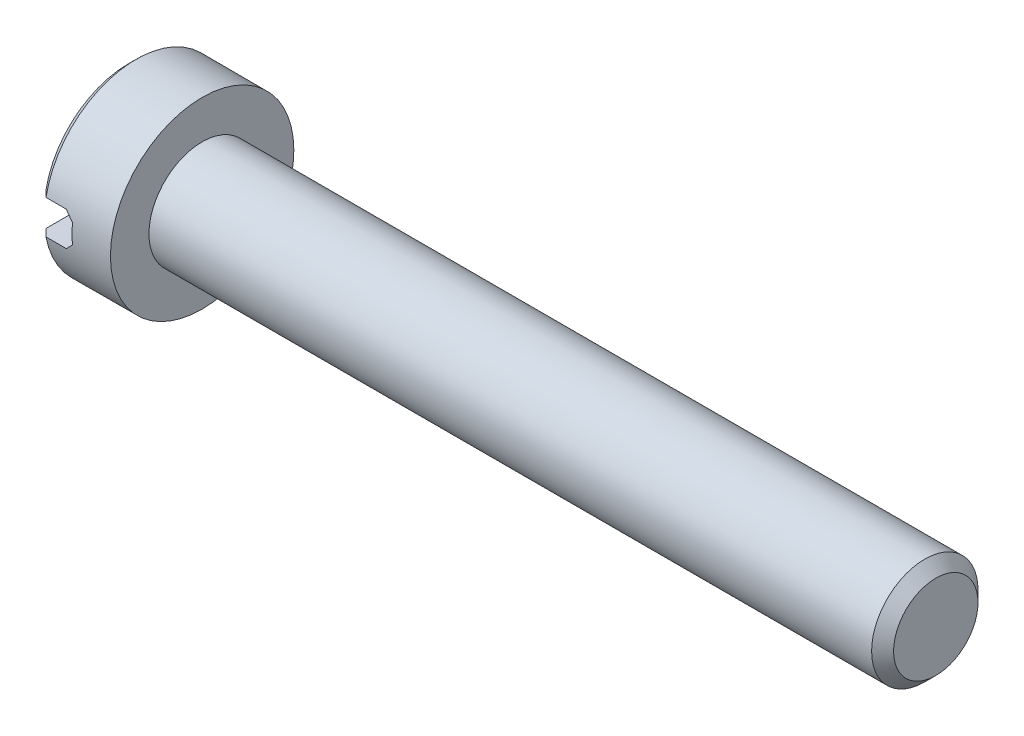
SolidWorks part; units mm, degrees
ref_plane "Face" through (0, 0, 0) normal (0, 0, 1) x (1, 0, 0)
ref_plane "Dessus" through (0, 0, 0) normal (0, 1, 0) x (1, 0, 0)
ref_plane "Droite" through (0, 0, 0) normal (1, 0, 0) x (0, 0, -1)
sketch "Esquisse1" plane through (0, 0, 0) normal (0, 0, 1) x (1, 0, 0)
  line L0 (0, 0) -> (0, 2.3)
  line L1 (0.2, 2.5) -> (2, 2.5)
  line L2 (2, 2.5) -> (2, 0)
  line L5 (0, 0) -> (7.6423, 0) construction
  line L7 (0, 2.3) -> (0.2, 2.5)
  line L8 (0, 0) -> (2, 0)
  point P1 (0, 2.5)
  dimension "D1" = 2.5
  dimension "D3" = 2
  dimension "D9" = 0.2
revolve "Révolution1" add sketch "Esquisse1" angle 360 about L5
sketch "Esquisse2" plane through (0, 0, 0) normal (0, 0, 1) x (1, 0, 0)
  line L0 (0, 2.3) -> (0, -2.3) construction
  line L1 (0, 0.4655) -> (0.7534, 0.4655)
  line L2 (0, 0.4655) -> (0, -0.4655)
  line L3 (0, -0.4655) -> (0.7534, -0.4655)
  line L4 (0.9534, 0.2655) -> (0.9534, -0.2655)
  line L5 (0.7534, 0.4655) -> (0.9534, 0.2655)
  line L6 (0.7534, -0.4655) -> (0.9534, -0.2655)
  point P1 (0.9534, -0.4655)
  point P3 (0.9534, 0.4655)
  dimension "D3" = 0.2
  dimension "D4" = 0.2
extrude "Enlèv. mat.-Extru.1" cut sketch "Esquisse2" against normal mid plane 10
sketch "Esquisse3" plane through (2, 0, 0) normal (1, 0, 0) x (0, 0, -1)
  circle A0 centre (0, 0) radius 1.45
extrude "Extrusion1" add sketch "Esquisse3" along normal blind 20
chamfer "Chanfrein1" distance 0.3 angle 45 1 edges at (22, 0, -1.45)
